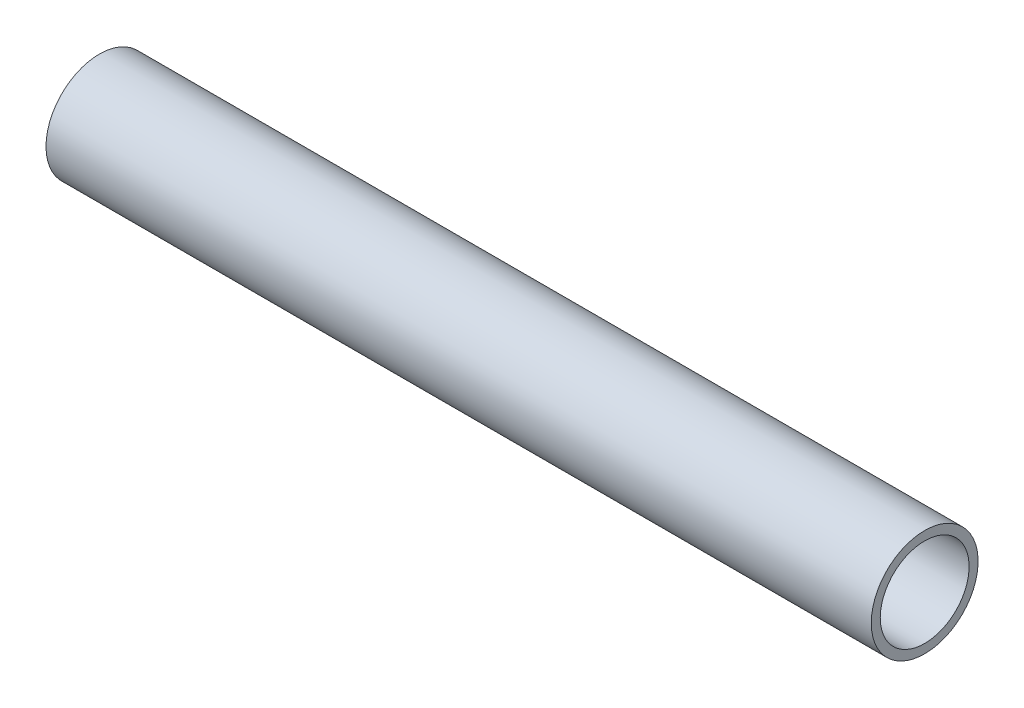
SolidWorks part; units mm, degrees
ref_plane "Front Plane" through (0, 0, 0) normal (0, 0, 1) x (1, 0, 0)
ref_plane "Top Plane" through (0, 0, 0) normal (0, 1, 0) x (1, 0, 0)
ref_plane "Right Plane" through (0, 0, 0) normal (1, 0, 0) x (0, 0, -1)
sketch "Sketch1" plane through (0, 0, 0) normal (0, 0, 1) x (1, 0, 0)
  line L0 (123.3016, 668.6998) -> (25.2028, 668.6998)
  point P2 (123.3016, 668.6998)
other "Pipe 0.5 SCH 40(1)"
ref_plane "Plane1" through (123.3016, 668.6998, 0) normal (-1, 0, 0) x (0, -1, 0)
sketch "Sketch11" plane through (123.3016, 668.6998, 0) normal (-1, 0, 0) x (0, -1, 0)
  circle A0 centre (0, 0) radius 5.2832
  circle A1 centre (0, 0) radius 6.35
  point P5 (0, 0)
  dimension "D1" = 12.7
  dimension "D2" = 10.5664
